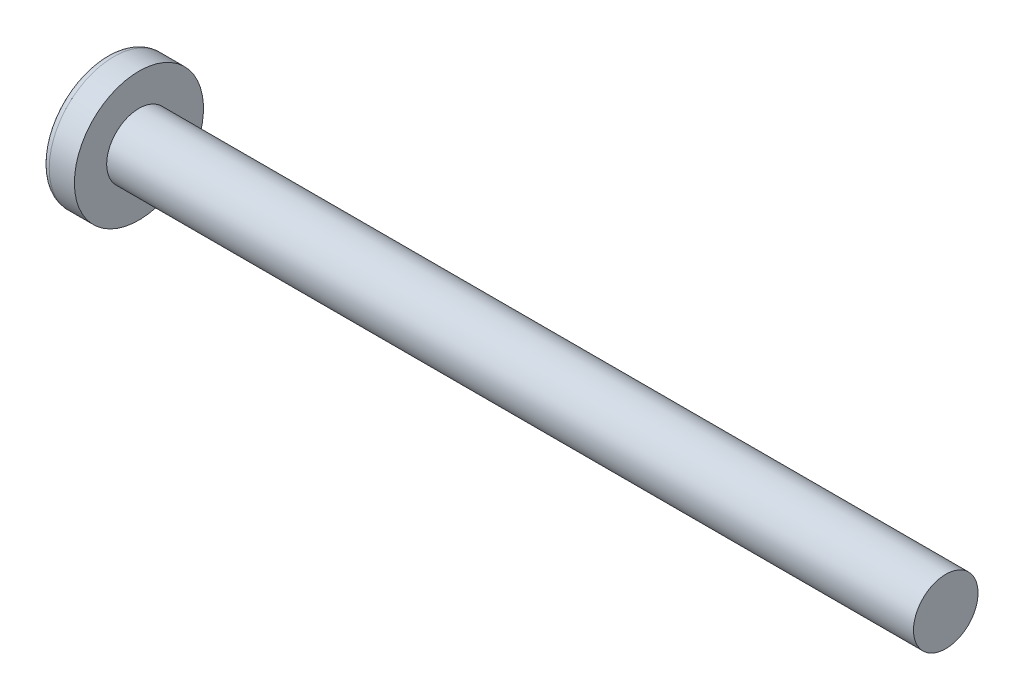
SolidWorks part; units mm, degrees
material "Plain Carbon Steel"
ref_plane "Plane1" through (0, 0, 0) normal (0, 0, 1) x (1, 0, 0)
ref_plane "Plane2" through (0, 0, 0) normal (0, 1, 0) x (1, 0, 0)
ref_plane "Plane3" through (0, 0, 0) normal (1, 0, 0) x (0, 0, -1)
sketch "BodySke" plane through (0, 0, 0) normal (0, 0, 1) x (1, 0, 0)
  line L0 (1.6, 1) -> (1.6, 2)
  line L1 (2, 6.35) -> (2, -3.175) construction
  line L2 (-25.4, 0) -> (127, 0) construction
  line L3 (26.6, 0) -> (0, 0)
  line L4 (1.6, 1) -> (26.6, 1)
  line L5 (26.6, 1) -> (26.6, 0)
  line L6 (0.8201, 2) -> (1.6, 2)
  line L7 (1.6, -1) -> (26.6, -1) construction
  line L8 (1.6, 6.35) -> (1.6, -3.175) construction
  arc A0 (0.6271, 1.9027) -> (0, 0) centre (3.2, 0) ccw
  arc A2 (0.6271, 1.9027) -> (0.8201, 2) centre (0.8201, 1.76) cw
  dimension "Head_crown_rad" = 3.2
  dimension "Head_fillet_rad" = 0.24
  dimension "Diameter" = 2
  dimension "Length" = 25
  dimension "Head_ht" = 1.6
  dimension "Head_dia" = 4
  dimension "Advance" = 0.4
  dimension "Thread_nom" = 25
revolve "Base-Revolve" add sketch "BodySke" angle 360 about L2
cosmetic thread "ThreadCosmetic" [suppressed] parameters "Thread_length"=24.6, "Thread_minor"=1.548
sketch "Sketch3" plane through (0, 0, 0) normal (1, 0, 0) x (0, 0, -1)
  line L0 (0.24, -0.91) -> (-0.24, -0.91)
  line L1 (0.24, -0.91) -> (0.24, 0.91)
  line L2 (-0.24, 0.91) -> (0.24, 0.91)
  line L3 (-0.24, 0.91) -> (-0.24, -0.91)
  dimension "Cross_dia" = 1.82
  dimension "D1" = 0.91
  dimension "Cross_width" = 0.48
  dimension "D2" = 0.24
ref_plane "Plane4" through (1.19, 0, 0) normal (1, 0, 0) x (0, 0, -1)
sketch "Sketch4" plane through (1.19, 0, 0) normal (1, 0, 0) x (0, 0, -1)
  line L0 (0.12, -0.12) -> (-0.12, -0.12)
  line L1 (0.12, -0.12) -> (0.12, 0.12)
  line L2 (-0.12, 0.12) -> (0.12, 0.12)
  line L3 (-0.12, 0.12) -> (-0.12, -0.12)
  dimension "D2" = 0.24
  dimension "D1" = 0.24
  dimension "D3" = 0.12
  dimension "D4" = 0.12
loft "Cut-Loft1" cut profiles "Sketch3", "Sketch4"
pattern_circular "CirPattern1" count 2 every 90 about axis through (0, 0, 0) along (1, 0, 0) of "Cut-Loft1"
sketch "ThdSchSke" plane through (0, 0, 0) normal (0, 0, 1) x (1, 0, 0)
  line L0 (2, -0.774) -> (1.8418, -1)
  line L1 (2, -0.774) -> (2.1582, -1)
  line L2 (2.1582, -1) -> (2.1582, -1.25)
  line L3 (-3.175, 0) -> (5.1513, 0) construction
  line L5 (2.1582, -1.25) -> (1.8418, -1.25)
  line L6 (1.8418, -1.25) -> (1.8418, -1)
  dimension "Diameter" = 2
  dimension "SideAngle" = 55
  dimension "VeeAngle" = 70
  dimension "Thread_minor" = 1.548
  dimension "Overcut" = 2.5
  dimension "Start" = 2
revolve "ThreadSchematic" [suppressed] cut sketch "ThdSchSke" angle 360 about L3
pattern_linear "ThdSchPat" [suppressed]
equation "\"D1@Sketch3\" = \"Cross_dia@Sketch3\" / 2"
equation "\"D2@Sketch3\" = \"Cross_width@Sketch3\" / 2"
equation "\"D1@Sketch4\" = \"Cross_width@Sketch3\" *.5"
equation "\"D2@Sketch4\" = \"D1@Sketch4\""
equation "\"D3@Sketch4\" = \"D1@Sketch4\" / 2"
equation "\"D4@Sketch4\" = \"D2@Sketch4\" / 2"
equation "\"Thread_length@ThreadCosmetic\" = ((sgn( (\"Length@BodySke\" - \"Advance@BodySke\" ) - \"Thread_nom@BodySke\" )-1)*( (\"Length@BodySke\" - \"Advance@BodySke\" ) - \"Thread_nom@BodySke\" ))/-2+ \"Thread_nom@BodySke\""
equation "\"Thread_minor@ThdSchSke\" = \"Thread_minor@ThreadCosmetic\""
equation "\"Diameter@ThdSchSke\" = \"Diameter@BodySke\""
equation "\"Overcut@ThdSchSke\" = \"Diameter@BodySke\" * 1.25"
equation "\"Start@ThdSchSke\" = \"Head_ht@BodySke\" + \"Length@BodySke\" - \"Thread_length@ThreadCosmetic\"  '---Non-countersunk---"
equation "\"Num_threads@ThdSchPat\" = int( \"Thread_length@ThreadCosmetic\" / \"Advance@BodySke\" + 0.999 )  + 1"
equation "\"Advance@ThdSchPat\" = \"Thread_length@ThreadCosmetic\" /  (\"Num_threads@ThdSchPat\" - 1) 'relax it"
